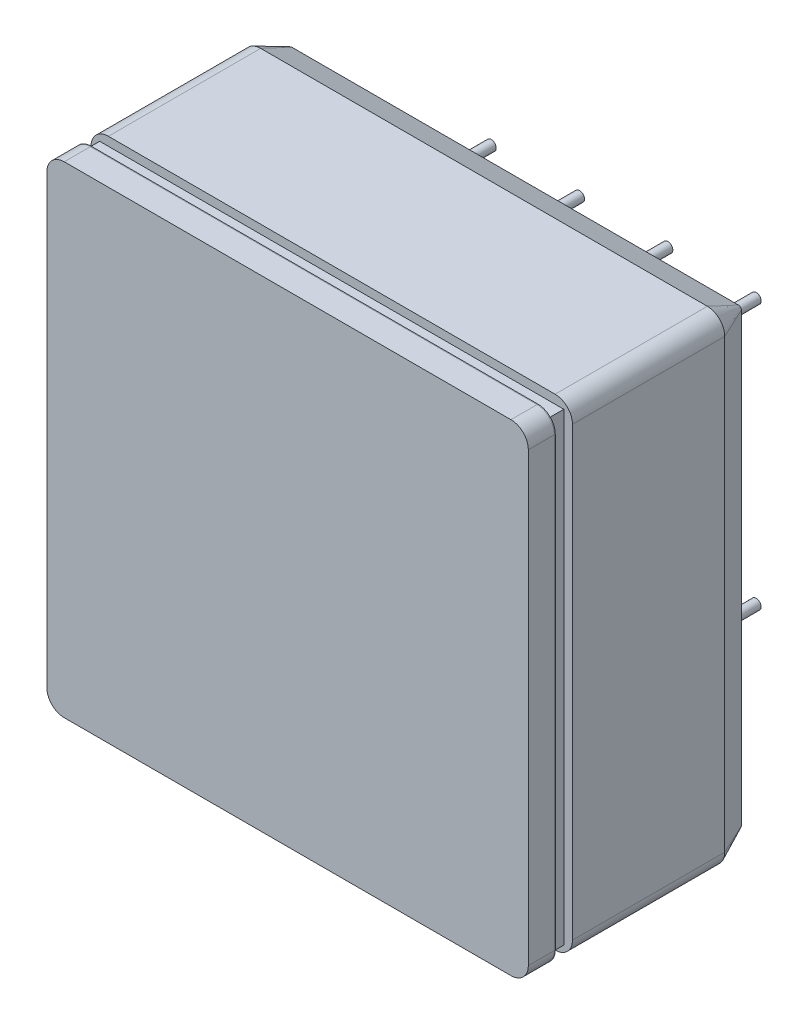
SolidWorks part; units mm, degrees
ref_plane "Front Plane" through (0, 0, 0) normal (0, 0, 1) x (1, 0, 0)
ref_plane "Top Plane" through (0, 0, 0) normal (0, 1, 0) x (1, 0, 0)
ref_plane "Right Plane" through (0, 0, 0) normal (1, 0, 0) x (0, 0, -1)
sketch "Sketch1" plane through (0, 0, 0) normal (0, 0, 1) x (1, 0, 0)
  line L1 (0, 0) -> (27.7, 0) construction
  line L2 (0, 0) -> (0, 27.7) construction
  line L3 (0, 27.7) -> (27.7, 27.7) construction
  line L4 (27.7, 0) -> (27.7, 27.7) construction
  line L5 (0.5, 0.5) -> (27.2, 0.5) construction
  line L6 (0.5, 0.5) -> (0.5, 27.2) construction
  line L7 (0.5, 27.2) -> (27.2, 27.2) construction
  line L8 (27.2, 0.5) -> (27.2, 27.2) construction
  line L9 (2.25, 2.25) -> (25.45, 2.25) construction
  line L10 (2.25, 2.25) -> (2.25, 25.45) construction
  line L11 (2.25, 25.45) -> (25.45, 25.45) construction
  line L12 (25.45, 2.25) -> (25.45, 25.45) construction
  line L13 (3.69, 3.69) -> (24.01, 3.69) construction
  line L14 (3.69, 3.69) -> (3.69, 24.01) construction
  line L15 (3.69, 24.01) -> (24.01, 24.01) construction
  line L16 (24.01, 3.69) -> (24.01, 24.01) construction
ref_plane "Plane1" through (0, 0, -2.54) normal (0, 0, 1) x (1, 0, 0)
sketch "Sketch2" plane through (0, 0, -2.54) normal (0, 0, 1) x (1, 0, 0)
  line L1 (1, 27.7) -> (26.7, 27.7)
  line L2 (0, 26.7) -> (0, 1)
  line L3 (1, 0) -> (26.7, 0)
  line L4 (27.7, 26.7) -> (27.7, 1)
  arc A0 (0, 1) -> (1, 0) centre (1, 1) ccw
  arc A1 (27.7, 1) -> (26.7, 0) centre (26.7, 1) cw
  arc A2 (27.7, 26.7) -> (26.7, 27.7) centre (26.7, 26.7) ccw
  arc A3 (1, 27.7) -> (0, 26.7) centre (1, 26.7) ccw
  dimension "D1" = 1
extrude "metal-case-at-HV" add sketch "Sketch2" against normal blind 8.76
sketch "Sketch3" plane through (0, 0, -2.54) normal (0, 0, 1) x (1, 0, 0)
  line L1 (1.3883, 26.1956) -> (26.126, 26.1956)
  line L2 (1.3883, 26.1956) -> (1.3883, 1.3651)
  line L3 (1.3883, 1.3651) -> (26.126, 1.3651)
  line L4 (26.126, 26.1956) -> (26.126, 1.3651)
extrude "photocathode" add sketch "Sketch3" along normal blind 0.1
sketch "Sketch5" plane through (0, 0, -2.54) normal (0, 0, 1) x (1, 0, 0)
  line L1 (0.5, 27.2) -> (27.2, 27.2)
  line L2 (0.5, 27.2) -> (0.5, 0.5)
  line L3 (0.5, 0.5) -> (27.2, 0.5)
  line L4 (27.2, 27.2) -> (27.2, 0.5)
  line L5 (2.25, 25.45) -> (25.45, 25.45)
  line L6 (2.25, 25.45) -> (2.25, 2.25)
  line L7 (2.25, 2.25) -> (25.45, 2.25)
  line L8 (25.45, 25.45) -> (25.45, 2.25)
extrude "Boss-Extrude3" add sketch "Sketch5" along normal blind 0.99
sketch "Sketch6" plane through (0, 0, -1.55) normal (0, 0, 1) x (1, 0, 0)
  line L1 (1, 27.7) -> (26.7, 27.7)
  line L2 (0, 26.7) -> (0, 1)
  line L3 (1, 0) -> (26.7, 0)
  line L4 (27.7, 26.7) -> (27.7, 1)
  line L5 (2.25, 25.45) -> (25.45, 25.45)
  line L6 (2.25, 25.45) -> (2.25, 2.25)
  line L7 (2.25, 2.25) -> (25.45, 2.25)
  line L8 (25.45, 25.45) -> (25.45, 2.25)
  arc A0 (0, 26.7) -> (1, 27.7) centre (1, 26.7) cw
  arc A1 (0, 1) -> (1, 0) centre (1, 1) ccw
  arc A2 (26.7, 0) -> (27.7, 1) centre (26.7, 1) ccw
  arc A3 (27.7, 26.7) -> (26.7, 27.7) centre (26.7, 26.7) ccw
  point P14 (0, 27.7)
  point P19 (27.7, 0)
  dimension "D1" = 1
  dimension "D2" = 1
extrude "mirrored-surface" add sketch "Sketch6" along normal blind 0.05
sketch "Sketch7" plane through (0, 0, -1.5) normal (0, 0, 1) x (1, 0, 0)
  line L1 (1, 27.7) -> (26.7, 27.7)
  line L2 (0, 26.7) -> (0, 1)
  line L3 (1, 0) -> (26.7, 0)
  line L4 (27.7, 26.7) -> (27.7, 1)
  arc A0 (0, 26.7) -> (1, 27.7) centre (1, 26.7) cw
  arc A1 (27.7, 26.7) -> (26.7, 27.7) centre (26.7, 26.7) ccw
  arc A2 (26.7, 0) -> (27.7, 1) centre (26.7, 1) ccw
  arc A3 (1, 0) -> (0, 1) centre (1, 1) cw
  point P9 (0, 27.7)
  point P13 (27.7, 0)
  dimension "D1" = 1
  dimension "D2" = 1
  dimension "D3" = 1
  dimension "D4" = 1
extrude "front-glass" add sketch "Sketch7" along normal blind 1.5 separate body
sketch "Sketch8" plane through (0, 0, -11.3) normal (0, 0, -1) x (-1, 0, 0)
  circle A0 centre (-24.01, 3.69) radius 0.285
  circle A1 centre (-21.47, 3.69) radius 0.285
  circle A2 centre (-18.93, 3.69) radius 0.285
  circle A3 centre (-16.39, 3.69) radius 0.285
  circle A4 centre (-13.85, 3.69) radius 0.285
  circle A5 centre (-11.31, 3.69) radius 0.285
  circle A6 centre (-8.77, 3.69) radius 0.285
  circle A7 centre (-6.23, 3.69) radius 0.285
  circle A8 centre (-3.69, 3.69) radius 0.285
  circle A9 centre (-24.01, 6.23) radius 0.285
  circle A10 centre (-21.47, 6.23) radius 0.285
  circle A11 centre (-18.93, 6.23) radius 0.285
  circle A12 centre (-16.39, 6.23) radius 0.285
  circle A13 centre (-13.85, 6.23) radius 0.285
  circle A14 centre (-11.31, 6.23) radius 0.285
  circle A15 centre (-8.77, 6.23) radius 0.285
  circle A16 centre (-6.23, 6.23) radius 0.285
  circle A17 centre (-3.69, 6.23) radius 0.285
  circle A18 centre (-24.01, 8.77) radius 0.285
  circle A19 centre (-21.47, 8.77) radius 0.285
  circle A20 centre (-18.93, 8.77) radius 0.285
  circle A21 centre (-16.39, 8.77) radius 0.285
  circle A22 centre (-13.85, 8.77) radius 0.285
  circle A23 centre (-11.31, 8.77) radius 0.285
  circle A24 centre (-8.77, 8.77) radius 0.285
  circle A25 centre (-6.23, 8.77) radius 0.285
  circle A26 centre (-3.69, 8.77) radius 0.285
  circle A27 centre (-24.01, 11.31) radius 0.285
  circle A28 centre (-21.47, 11.31) radius 0.285
  circle A29 centre (-18.93, 11.31) radius 0.285
  circle A30 centre (-16.39, 11.31) radius 0.285
  circle A31 centre (-13.85, 11.31) radius 0.285
  circle A32 centre (-11.31, 11.31) radius 0.285
  circle A33 centre (-8.77, 11.31) radius 0.285
  circle A34 centre (-6.23, 11.31) radius 0.285
  circle A35 centre (-3.69, 11.31) radius 0.285
  circle A36 centre (-24.01, 13.85) radius 0.285
  circle A37 centre (-21.47, 13.85) radius 0.285
  circle A38 centre (-18.93, 13.85) radius 0.285
  circle A39 centre (-16.39, 13.85) radius 0.285
  circle A40 centre (-13.85, 13.85) radius 0.285
  circle A41 centre (-11.31, 13.85) radius 0.285
  circle A42 centre (-8.77, 13.85) radius 0.285
  circle A43 centre (-6.23, 13.85) radius 0.285
  circle A44 centre (-3.69, 13.85) radius 0.285
  circle A45 centre (-24.01, 16.39) radius 0.285
  circle A46 centre (-21.47, 16.39) radius 0.285
  circle A47 centre (-18.93, 16.39) radius 0.285
  circle A48 centre (-16.39, 16.39) radius 0.285
  circle A49 centre (-13.85, 16.39) radius 0.285
  circle A50 centre (-11.31, 16.39) radius 0.285
  circle A51 centre (-8.77, 16.39) radius 0.285
  circle A52 centre (-6.23, 16.39) radius 0.285
  circle A53 centre (-3.69, 16.39) radius 0.285
  circle A54 centre (-24.01, 18.93) radius 0.285
  circle A55 centre (-21.47, 18.93) radius 0.285
  circle A56 centre (-18.93, 18.93) radius 0.285
  circle A57 centre (-16.39, 18.93) radius 0.285
  circle A58 centre (-13.85, 18.93) radius 0.285
  circle A59 centre (-11.31, 18.93) radius 0.285
  circle A60 centre (-8.77, 18.93) radius 0.285
  circle A61 centre (-6.23, 18.93) radius 0.285
  circle A62 centre (-3.69, 18.93) radius 0.285
  circle A63 centre (-24.01, 21.47) radius 0.285
  circle A64 centre (-21.47, 21.47) radius 0.285
  circle A65 centre (-18.93, 21.47) radius 0.285
  circle A66 centre (-16.39, 21.47) radius 0.285
  circle A67 centre (-13.85, 21.47) radius 0.285
  circle A68 centre (-11.31, 21.47) radius 0.285
  circle A69 centre (-8.77, 21.47) radius 0.285
  circle A70 centre (-6.23, 21.47) radius 0.285
  circle A71 centre (-3.69, 21.47) radius 0.285
  circle A72 centre (-24.01, 24.01) radius 0.285
  circle A73 centre (-21.47, 24.01) radius 0.285
  circle A74 centre (-18.93, 24.01) radius 0.285
  circle A75 centre (-16.39, 24.01) radius 0.285
  circle A76 centre (-13.85, 24.01) radius 0.285
  circle A77 centre (-11.31, 24.01) radius 0.285
  circle A78 centre (-8.77, 24.01) radius 0.285
  circle A79 centre (-6.23, 24.01) radius 0.285
  circle A80 centre (-3.69, 24.01) radius 0.285
extrude "pins" add sketch "Sketch8" along normal blind 5.5
sketch "Sketch9" plane through (0, 0, -16.8) normal (0, 0, -1) x (-1, 0, 0)
  line L0 (-22.1816, 24.8612) -> (-20.7784, 24.8612)
  line L1 (-22.1816, 24.8612) -> (-22.1816, 23.3649)
  line L2 (-22.1816, 23.3649) -> (-20.7784, 23.3649)
  line L3 (-20.7784, 24.8612) -> (-20.7784, 23.3649)
  line L4 (-17.3107, 24.8612) -> (-15.8078, 24.8612)
  line L5 (-17.3107, 24.8612) -> (-17.3107, 22.981)
  line L6 (-17.3107, 22.981) -> (-15.8078, 22.981)
  line L7 (-15.8078, 24.8612) -> (-15.8078, 22.981)
  line L8 (-11.8655, 24.8612) -> (-10.4335, 24.8612)
  line L9 (-11.8655, 24.8612) -> (-11.8655, 22.981)
  line L10 (-11.8655, 22.981) -> (-10.4335, 22.981)
  line L11 (-10.4335, 24.8612) -> (-10.4335, 22.981)
  line L12 (-7.2079, 24.8612) -> (-2.98, 24.8612)
  line L13 (-7.2079, 24.8612) -> (-7.2079, 23.3649)
  line L14 (-7.2079, 23.3649) -> (-2.98, 23.3649)
  line L15 (-2.98, 24.8612) -> (-2.98, 23.3649)
  line L16 (-24.8835, 22.2271) -> (-23.0472, 22.2271)
  line L17 (-24.8835, 22.2271) -> (-24.8835, 10.532)
  line L18 (-24.8835, 10.532) -> (-23.0472, 10.532)
  line L19 (-23.0472, 22.2271) -> (-23.0472, 10.532)
  line L20 (-24.8835, 7.577) -> (-23.0472, 7.577)
  line L21 (-24.8835, 7.577) -> (-24.8835, 2.706)
  line L22 (-24.8835, 2.706) -> (-23.0472, 2.706)
  line L23 (-23.0472, 7.577) -> (-23.0472, 2.706)
  line L24 (-19.7935, 22.4499) -> (-17.9649, 22.4499)
  line L25 (-19.7935, 22.4499) -> (-19.7935, 20.7304)
  line L26 (-19.7935, 20.7304) -> (-17.9649, 20.7304)
  line L27 (-17.9649, 22.4499) -> (-17.9649, 20.7304)
  line L28 (-14.5667, 22.4499) -> (-12.9507, 22.4499)
  line L29 (-14.5667, 22.4499) -> (-14.5667, 20.7304)
  line L30 (-14.5667, 20.7304) -> (-12.9507, 20.7304)
  line L31 (-12.9507, 22.4499) -> (-12.9507, 20.7304)
  line L32 (-9.3756, 22.4499) -> (-8.0103, 22.4499)
  line L33 (-9.3756, 22.4499) -> (-9.3756, 20.7304)
  line L34 (-9.3756, 20.7304) -> (-8.0103, 20.7304)
  line L35 (-8.0103, 22.4499) -> (-8.0103, 20.7304)
  line L36 (-4.5054, 22.2271) -> (-2.98, 22.2271)
  line L37 (-4.5054, 22.2271) -> (-4.5054, 20.7304)
  line L38 (-4.5054, 20.7304) -> (-2.98, 20.7304)
  line L39 (-2.98, 22.2271) -> (-2.98, 20.7304)
  line L40 (-22.4238, 19.8145) -> (-5.3688, 19.8145)
  line L41 (-22.4238, 19.8145) -> (-22.4238, 18.3702)
  line L42 (-22.4238, 18.3702) -> (-5.3688, 18.3702)
  line L43 (-5.3688, 19.8145) -> (-5.3688, 18.3702)
  line L44 (-22.4238, 14.7607) -> (-5.3688, 14.7607)
  line L45 (-22.4238, 14.7607) -> (-22.4238, 13.143)
  line L46 (-22.4238, 13.143) -> (-5.3688, 13.143)
  line L47 (-5.3688, 14.7607) -> (-5.3688, 13.143)
  line L48 (-22.4238, 9.6389) -> (-5.3688, 9.6389)
  line L49 (-22.4238, 9.6389) -> (-22.4238, 8.1251)
  line L50 (-22.4238, 8.1251) -> (-5.3688, 8.1251)
  line L51 (-5.3688, 9.6389) -> (-5.3688, 8.1251)
  line L52 (-4.5054, 17.5985) -> (-2.98, 17.5985)
  line L53 (-4.5054, 17.5985) -> (-4.5054, 2.706)
  line L54 (-4.5054, 2.706) -> (-2.98, 2.706)
  line L55 (-2.98, 17.5985) -> (-2.98, 2.706)
  line L56 (-19.7935, 17.3274) -> (-17.9649, 17.3274)
  line L57 (-19.7935, 17.3274) -> (-19.7935, 15.6815)
  line L58 (-19.7935, 15.6815) -> (-17.9649, 15.6815)
  line L59 (-17.9649, 17.3274) -> (-17.9649, 15.6815)
  line L60 (-14.5667, 17.3274) -> (-12.9507, 17.3274)
  line L61 (-14.5667, 17.3274) -> (-14.5667, 15.6815)
  line L62 (-14.5667, 15.6815) -> (-12.9507, 15.6815)
  line L63 (-12.9507, 17.3274) -> (-12.9507, 15.6815)
  line L64 (-9.3756, 17.3274) -> (-8.0103, 17.3274)
  line L65 (-9.3756, 17.3274) -> (-9.3756, 15.6815)
  line L66 (-9.3756, 15.6815) -> (-8.0103, 15.6815)
  line L67 (-8.0103, 17.3274) -> (-8.0103, 15.6815)
  line L68 (-9.3756, 12.3613) -> (-8.0103, 12.3613)
  line L69 (-9.3756, 12.3613) -> (-9.3756, 10.532)
  line L70 (-9.3756, 10.532) -> (-8.0103, 10.532)
  line L71 (-8.0103, 12.3613) -> (-8.0103, 10.532)
  line L72 (-9.3756, 7.021) -> (-8.2349, 7.021)
  line L73 (-9.3756, 7.021) -> (-9.3756, 5.5289)
  line L74 (-9.3756, 5.5289) -> (-8.2349, 5.5289)
  line L75 (-8.2349, 7.021) -> (-8.2349, 5.5289)
  line L76 (-14.9745, 7.021) -> (-13.2505, 7.021)
  line L77 (-14.9745, 7.021) -> (-14.9745, 5.5289)
  line L78 (-14.9745, 5.5289) -> (-13.2505, 5.5289)
  line L79 (-13.2505, 7.021) -> (-13.2505, 5.5289)
  line L80 (-14.5667, 12.1026) -> (-13.2505, 12.1026)
  line L81 (-14.5667, 12.1026) -> (-14.5667, 10.532)
  line L82 (-14.5667, 10.532) -> (-13.2505, 10.532)
  line L83 (-13.2505, 12.1026) -> (-13.2505, 10.532)
  line L84 (-19.7935, 12.3613) -> (-18.2001, 12.3613)
  line L85 (-19.7935, 12.3613) -> (-19.7935, 10.532)
  line L86 (-19.7935, 10.532) -> (-18.2001, 10.532)
  line L87 (-18.2001, 12.3613) -> (-18.2001, 10.532)
  line L88 (-19.7935, 7.021) -> (-17.9649, 7.021)
  line L89 (-19.7935, 7.021) -> (-19.7935, 5.5289)
  line L90 (-19.7935, 5.5289) -> (-17.9649, 5.5289)
  line L91 (-17.9649, 7.021) -> (-17.9649, 5.5289)
  line L92 (-22.4238, 4.9123) -> (-20.5348, 4.9123)
  line L93 (-22.4238, 4.9123) -> (-22.4238, 2.706)
  line L94 (-22.4238, 2.706) -> (-20.5348, 2.706)
  line L95 (-20.5348, 4.9123) -> (-20.5348, 2.706)
  line L96 (-17.3107, 4.4899) -> (-10.4335, 4.4899)
  line L97 (-17.3107, 4.4899) -> (-17.3107, 2.706)
  line L98 (-17.3107, 2.706) -> (-10.4335, 2.706)
  line L99 (-10.4335, 4.4899) -> (-10.4335, 2.706)
  line L100 (-7.5372, 4.4899) -> (-5.7773, 4.4899)
  line L101 (-7.5372, 4.4899) -> (-7.5372, 3.0088)
  line L102 (-7.5372, 3.0088) -> (-5.7773, 3.0088)
  line L103 (-5.7773, 4.4899) -> (-5.7773, 3.0088)
extrude "Cut-Extrude1" cut sketch "Sketch9" against normal blind 5.5
sketch "Sketch10" plane through (0, 0, -11.3) normal (0, 0, -1) x (-1, 0, 0)
  line L1 (-26.7, 27.7) -> (-1, 27.7)
  line L2 (-27.7, 26.7) -> (-27.7, 1)
  line L3 (-26.7, 0) -> (-1, 0)
  line L4 (0, 26.7) -> (0, 1)
  arc A0 (-26.7, 0) -> (-27.7, 1) centre (-26.7, 1) cw
  arc A1 (0, 26.7) -> (-1, 27.7) centre (-1, 26.7) ccw
  arc A2 (0, 1) -> (-1, 0) centre (-1, 1) cw
  arc A3 (-27.7, 26.7) -> (-26.7, 27.7) centre (-26.7, 26.7) cw
  point P11 (0, 0)
  dimension "D1" = 1
extrude "rubber" add sketch "Sketch10" along normal blind 1.79 draft 25 separate body
sketch "Sketch11" plane through (0, 0, -16.8) normal (0, 0, -1) x (-1, 0, 0)
  line L1 (-26.7, 27.7) -> (-1, 27.7) construction
  line L2 (-27.7, 26.7) -> (-27.7, 1) construction
  line L3 (-26.7, 0) -> (-1, 0) construction
  line L4 (0, 26.7) -> (0, 1) construction
  circle A0 centre (-24.01, 24.01) radius 0.285
  circle A1 centre (-18.93, 24.01) radius 0.285
  circle A2 centre (-13.85, 24.01) radius 0.285
  circle A3 centre (-8.77, 24.01) radius 0.285
  circle A4 centre (-6.23, 21.47) radius 0.285
  circle A5 centre (-11.31, 21.47) radius 0.285
  circle A6 centre (-16.39, 21.47) radius 0.285
  circle A7 centre (-21.47, 21.47) radius 0.285
  circle A8 centre (-21.47, 16.39) radius 0.285
  circle A9 centre (-16.39, 16.39) radius 0.285
  circle A10 centre (-11.31, 16.39) radius 0.285
  circle A11 centre (-6.23, 16.39) radius 0.285
  circle A12 centre (-3.69, 18.93) radius 0.285
  circle A13 centre (-21.47, 11.31) radius 0.285
  circle A14 centre (-16.39, 11.31) radius 0.285
  circle A15 centre (-11.31, 11.31) radius 0.285
  circle A16 centre (-6.23, 11.31) radius 0.285
  circle A17 centre (-24.01, 8.77) radius 0.285
  circle A18 centre (-21.47, 6.23) radius 0.285
  arc A19 (-26.7, 27.7) -> (-27.7, 26.7) centre (-26.7, 26.7) ccw construction
  circle A20 centre (-11.31, 6.23) radius 0.285
  circle A21 centre (-6.23, 6.23) radius 0.285
  circle A22 centre (-8.77, 3.69) radius 0.285
  circle A23 centre (-18.93, 3.69) radius 0.285
  circle A24 centre (-16.39, 6.23) radius 0.285
  arc A25 (-27.7, 1) -> (-26.7, 0) centre (-26.7, 1) ccw construction
  arc A26 (0, 1) -> (-1, 0) centre (-1, 1) cw construction
  arc A27 (0, 26.7) -> (-1, 27.7) centre (-1, 26.7) ccw construction
  dimension "D1" = 1
  dimension "D2" = 1
